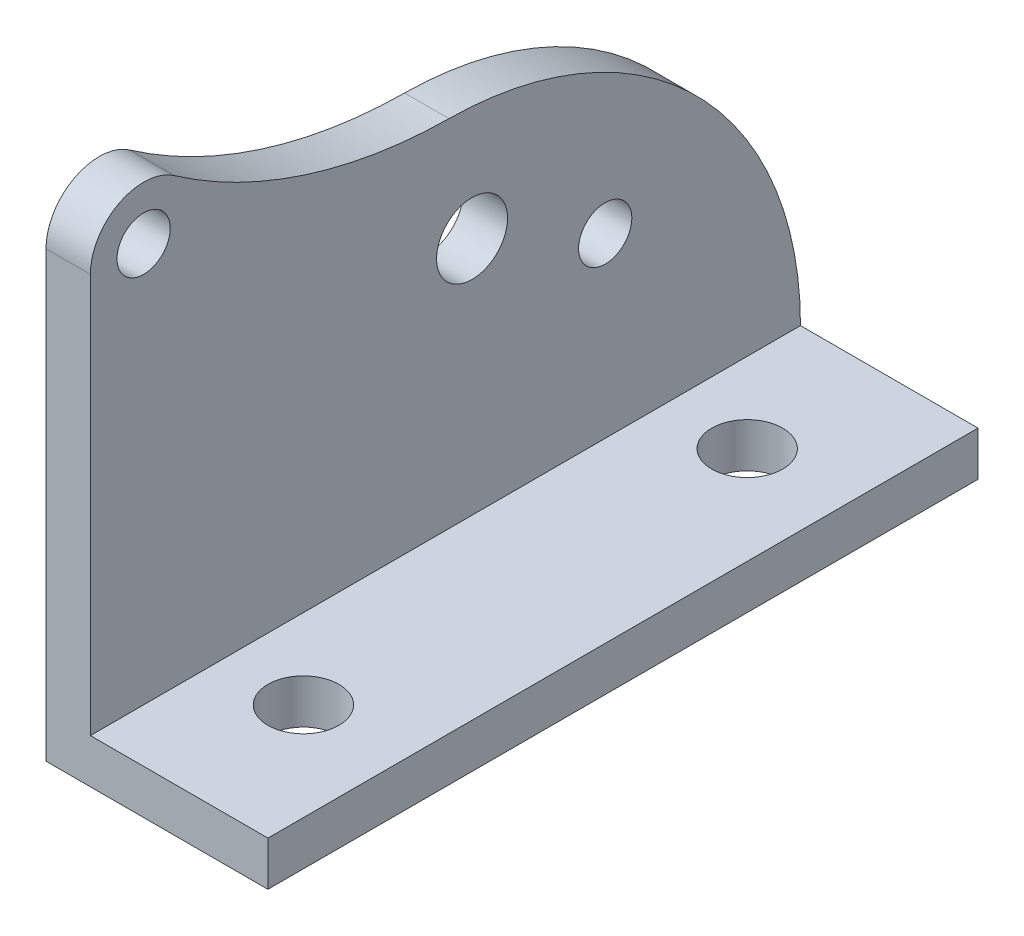
SolidWorks part; units mm, degrees
material "6061-T6 (SS)"
ref_plane "Front Plane" through (0, 0, 0) normal (0, 0, 1) x (1, 0, 0)
ref_plane "Top Plane" through (0, 0, 0) normal (0, 1, 0) x (1, 0, 0)
ref_plane "Right Plane" through (0, 0, 0) normal (1, 0, 0) x (0, 0, -1)
sketch "Sketch1" plane through (0, 0, 0) normal (1, 0, 0) x (0, 0, -1)
  line L1 (-40, 50) -> (40, 50)
  line L2 (-40, 50) -> (-40, -50)
  line L3 (-40, -50) -> (40, -50)
  line L4 (40, 50) -> (40, -50)
  line L5 (-40, 50) -> (40, -50) construction
  line L6 (-40, -50) -> (40, 50) construction
  point P0 (0, 0)
  dimension "D1" = 100
  dimension "D2" = 80
extrude "Boss-Extrude1" add sketch "Sketch1" along normal blind 5
sketch "Sketch2" plane through (5, 0, 0) normal (1, 0, 0) x (0, 0, -1)
  line L0 (40, -50) -> (40, 50) construction
  line L1 (-40, -50) -> (40, -50)
  line L2 (-40, -50) -> (-40, -45)
  line L3 (-40, -45) -> (40, -45)
  line L4 (40, -50) -> (40, -45)
  dimension "D1" = 5
extrude "Boss-Extrude2" add sketch "Sketch2" along normal blind 20
sketch "Sketch3" plane through (0, -45, 0) normal (0, 1, 0) x (1, 0, 0)
  line L1 (25, 40) -> (5, 40) construction
  line L2 (25, 40) -> (25, -40) construction
  line L3 (25, -40) -> (5, -40) construction
  circle A0 centre (14, 25) radius 4
  circle A1 centre (14, -25) radius 4
  dimension "D3" = 8
  dimension "D1" = 15
  dimension "D2" = 11
  dimension "D4" = 15
extrude "Cut-Extrude1" cut sketch "Sketch3" against normal through all
sketch "Sketch4" plane through (5, 0, 0) normal (1, 0, 0) x (0, 0, -1)
  line L3 (-40, -50) -> (40, -50) construction
  line L5 (40, -45) -> (40, 50) construction
  circle A0 centre (3, -18) radius 4
  dimension "D3" = 8
  dimension "D1" = 32
  dimension "D2" = 37
extrude "Cut-Extrude2" cut sketch "Sketch4" against normal through all
sketch "Sketch5" plane through (5, 0, 0) normal (1, 0, 0) x (0, 0, -1)
  line L0 (-40, -50) -> (40, -50) construction
  line L1 (0, 56.7) -> (0, -71.321) construction
  line L2 (40, -45) -> (40, 50) construction
  line L3 (40, 0) -> (40, -45) construction
  line L4 (-40, 0) -> (-40, -45)
  arc A0 (-40, -45) -> (40, -45) centre (0, -45) cw
  circle A1 centre (34, 0) radius 6 construction
  arc A2 (-0.3998, -5.002) -> (30.5623, 4.9176) centre (-0.9496, 49.9953) ccw construction
  circle A3 centre (34, 0) radius 3 construction
  circle A4 centre (-34, 0) radius 3
  circle A5 centre (-34, 0) radius 6
  arc A6 (0.3998, -5.002) -> (-30.5623, 4.9176) centre (0.9496, 49.9953) cw
  dimension "D1" = 40
  dimension "D2" = 12
  dimension "D4" = 55
  dimension "D5" = 6
  dimension "D3" = 50
extrude "Cut-Extrude4" cut sketch "Sketch5" against normal through all
sketch "Sketch6" plane through (25, 0, 0) normal (1, 0, 0) x (0, 0, -1)
  line L0 (-40, -50) -> (40, -50) construction
  line L1 (-45.067, 10) -> (54.933, 10)
  line L2 (-45.067, 10) -> (-45.067, -50)
  line L3 (-45.067, -50) -> (54.933, -50)
  line L4 (54.933, 10) -> (54.933, -50)
  dimension "D1" = 100
  dimension "D2" = 60
sketch "Sketch7" plane through (0, 0, 0) normal (-1, 0, 0) x (0, 0, 1)
  line L0 (40, -50) -> (-40, -50) construction
  line L1 (-40, -50) -> (-40, -45) construction
  circle A0 centre (-18, -25) radius 3
  dimension "D1" = 6
  dimension "D2" = 25
  dimension "D3" = 22
extrude "Cut-Extrude5" cut sketch "Sketch7" against normal blind 10
